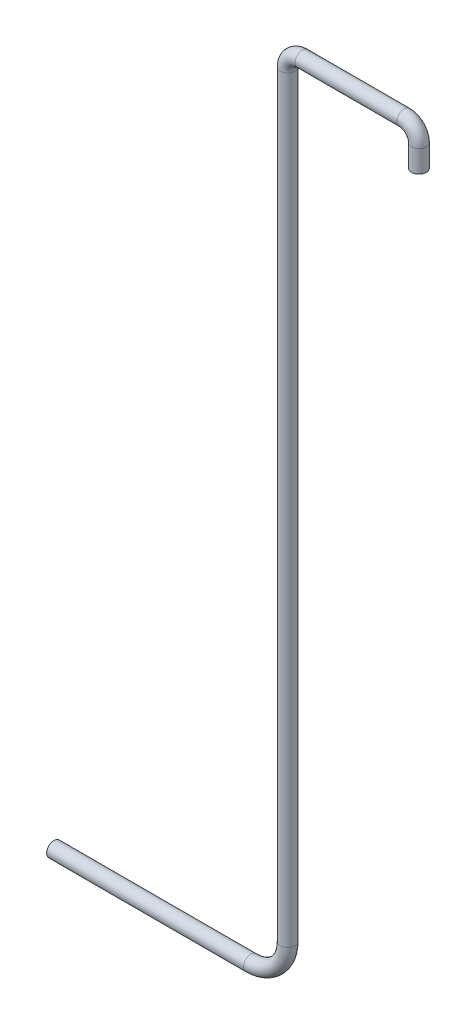
SolidWorks part; units mm, degrees
ref_plane "Plan de face" through (0, 0, 0) normal (0, 0, 1) x (1, 0, 0)
ref_plane "Plan de dessus" through (0, 0, 0) normal (0, 1, 0) x (1, 0, 0)
ref_plane "Plan de droite" through (0, 0, 0) normal (1, 0, 0) x (0, 0, -1)
sketch "Esquisse1" plane through (0, 0, 0) normal (0, 0, 1) x (1, 0, 0)
  line L0 (0, 0) -> (0, 0.3)
  line L1 (-0.2, 0.5) -> (-1.5845, 0.5)
  line L2 (-1.7845, 0.3) -> (-1.7845, -9.9924)
  line L3 (-2.2845, -10.4924) -> (-4.9602, -10.4924)
  arc A0 (-1.7845, 0.3) -> (-1.5845, 0.5) centre (-1.5845, 0.3) cw
  arc A1 (-0.2, 0.5) -> (0, 0.3) centre (-0.2, 0.3) cw
  arc A2 (-2.2845, -10.4924) -> (-1.7845, -9.9924) centre (-2.2845, -9.9924) ccw
  dimension "D1" = 0.2
  dimension "D2" = 0.5
sketch "Esquisse2" plane through (0, 0, 0) normal (0, 1, 0) x (1, 0, 0)
  circle A0 centre (0, 0) radius 0.1
sweep "Balayage1" add profiles "Esquisse2" path "Esquisse1"
